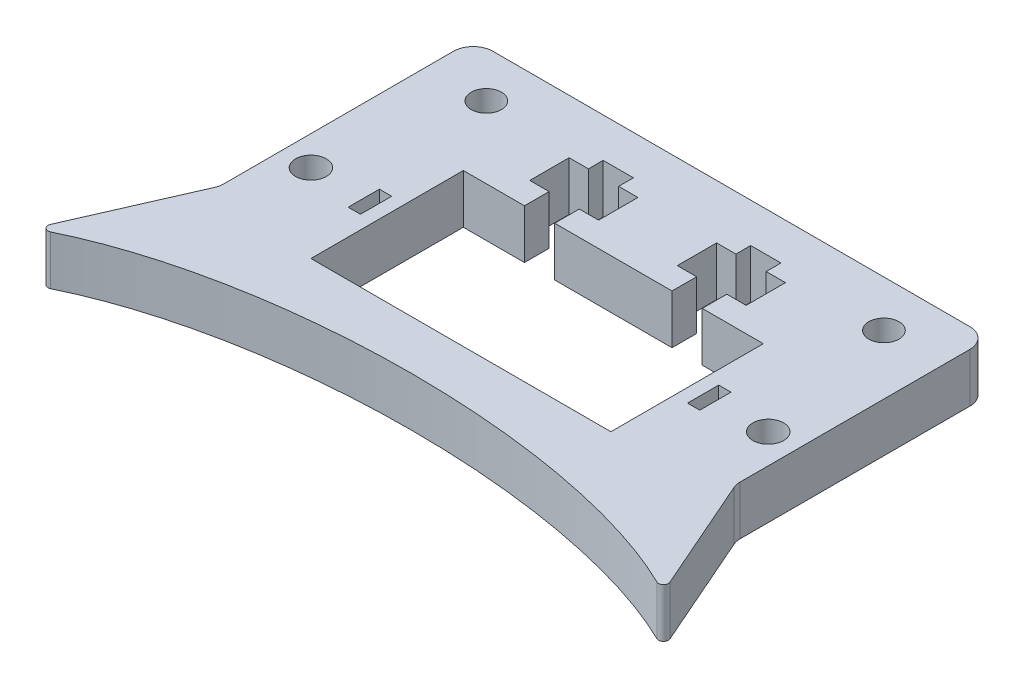
SolidWorks part; units mm, degrees
ref_plane "Front Plane" through (0, 0, 0) normal (0, 0, 1) x (1, 0, 0)
ref_plane "Top Plane" through (0, 0, 0) normal (0, 1, 0) x (1, 0, 0)
ref_plane "Right Plane" through (0, 0, 0) normal (1, 0, 0) x (0, 0, -1)
sketch "Sketch1" plane through (0, 0, 0) normal (0, 1, 0) x (1, 0, 0)
  line L1 (-52.5, -32.5) -> (52.5, -32.5)
  line L2 (-52.5, -32.5) -> (-52.5, 32.5)
  line L3 (-52.5, 32.5) -> (52.5, 32.5)
  line L4 (52.5, -32.5) -> (52.5, 32.5)
  line L5 (0, 32.5) -> (0, -32.5) construction
  line L6 (-52.5, 0) -> (52.5, 0) construction
  point P0 (0, 0)
  dimension "D1" = 105
  dimension "D2" = 65
extrude "Boss-Extrude1" add sketch "Sketch1" along normal blind 10
sketch "Sketch2" plane through (0, 10, 0) normal (0, 1, 0) x (1, 0, 0)
  line L6 (-30.5, 8.5) -> (30.5, 8.5)
  line L7 (-30.5, 8.5) -> (-30.5, -22.5)
  line L8 (-30.5, -22.5) -> (30.5, -22.5)
  line L9 (30.5, 8.5) -> (30.5, -22.5)
  line L10 (0, -22.5) -> (0, 8.5) construction
  line L11 (-30.5, -7) -> (30.5, -7) construction
  line L12 (0, 0) -> (0, -22.5) construction
  line L14 (-52.5, -32.5) -> (52.5, -32.5) construction
  point P0 (0, -7)
  dimension "D1" = 31
  dimension "D2" = 61
  dimension "D3" = 10
extrude "Cut-Extrude1" cut sketch "Sketch2" against normal through all
sketch "Sketch3" plane through (0, 10, 0) normal (0, 1, 0) x (1, 0, 0)
  line L0 (-15, 32.5) -> (-15, 9.5021) construction
  line L1 (52.5, 32.5) -> (-52.5, 32.5) construction
  line L3 (-22, 21.5) -> (-22, 13.5)
  line L4 (-18.075, 5.5043) -> (-11.925, 5.5043)
  line L5 (-18.075, 5.5043) -> (-18.075, 13.5)
  line L6 (-18.075, 13.5) -> (-11.925, 13.5)
  line L7 (-11.925, 5.5043) -> (-11.925, 13.5)
  line L8 (-15, 13.5) -> (-15, 5.5043) construction
  line L9 (-18.075, 9.5021) -> (-11.925, 9.5021) construction
  line L10 (-22, 21.5) -> (-8, 21.5)
  line L11 (-22, 13.5) -> (-8, 13.5)
  line L12 (-8, 21.5) -> (-8, 13.5)
  line L13 (-15, 13.5) -> (-15, 21.5) construction
  line L14 (-22, 17.5) -> (-8, 17.5) construction
  line L15 (0, 0) -> (0, 32.5) construction
  line L16 (-11.925, 18.5) -> (-18.075, 18.5)
  line L17 (-11.925, 18.5) -> (-11.925, 24.5)
  line L18 (-11.925, 24.5) -> (-18.075, 24.5)
  line L19 (-18.075, 18.5) -> (-18.075, 24.5)
  line L20 (-15, 24.5) -> (-15, 18.5) construction
  line L21 (-11.925, 21.5) -> (-18.075, 21.5) construction
  line L22 (30.5, 8.5) -> (-30.5, 8.5) construction
  point P10 (-15, 17.5)
  dimension "D1" = 6.15
  dimension "D2" = 5
  dimension "D3" = 14
  dimension "D4" = 8
  dimension "D5" = 16
  dimension "D6" = 15
extrude "Cut-Extrude2" cut sketch "Sketch3" against normal blind 10
sketch "Sketch4" plane through (0, 10, 0) normal (0, 1, 0) x (1, 0, 0)
  line L2 (-46.5, -6.5) -> (-34.5, -6.5) construction
  line L3 (-18.075, 8.5) -> (-30.5, 8.5) construction
  line L4 (-33.25, -3.325) -> (-35.75, -3.325)
  line L5 (-33.25, -3.325) -> (-33.25, -9.675)
  line L6 (-33.25, -9.675) -> (-35.75, -9.675)
  line L7 (-35.75, -3.325) -> (-35.75, -9.675)
  line L8 (-34.5, -9.675) -> (-34.5, -3.325) construction
  line L9 (-33.25, -6.5) -> (-35.75, -6.5) construction
  line L10 (-30.5, 8.5) -> (-30.5, -22.5) construction
  circle A0 centre (-46.5, -6.5) radius 3.125
  dimension "D1" = 6.25
  dimension "D2" = 15
  dimension "D3" = 16
  dimension "D4" = 2.5
  dimension "D5" = 6.35
  dimension "D6" = 2.75
extrude "Cut-Extrude3" cut sketch "Sketch4" against normal through all
sketch "Sketch5" plane through (0, 0, 0) normal (0, 1, 0) x (1, 0, 0)
  line L0 (0, 0) -> (0, -65) construction
  line L1 (-52.5, -32.5) -> (52.5, -32.5) construction
  line L2 (-52.5, -19.0391) -> (-64.12, -45.5652)
  line L3 (-52.5, 32.5) -> (-52.5, -32.5) construction
  line L4 (-52.5, -19.0391) -> (0, -32.5)
  ellipse E0 centre (0, -65) end of major axis (-80, -65) minor radius 32.5
  dimension "D1" = 160
  dimension "D2" = 65
extrude "Boss-Extrude2" add sketch "Sketch5" along normal up to surface (10 mm away) contours E0 L4 L2 up to face at (-46.5, 10, 9.625)
sketch "Sketch6" plane through (0, 10, 0) normal (0, 1, 0) x (1, 0, 0)
  circle A0 centre (-40.4209, 23.095) radius 3.075
  dimension "D1" = 6.15
extrude "Cut-Extrude4" cut sketch "Sketch6" against normal through all
mirror "Mirror1" about plane through (0, 0, 0) normal (1, 0, 0) of "Cut-Extrude4", "Cut-Extrude3", "Cut-Extrude2", "Boss-Extrude2"
fillet "Fillet2" radius 1 2 edges at (-64.12, 5, 45.5652) (64.12, 5, 45.5652)
fillet "Fillet1" radius 4 4 edges at (-52.5, 5, 19.0391) (-52.5, 5, -32.5) (52.5, 5, 19.0391) (52.5, 5, -32.5)
